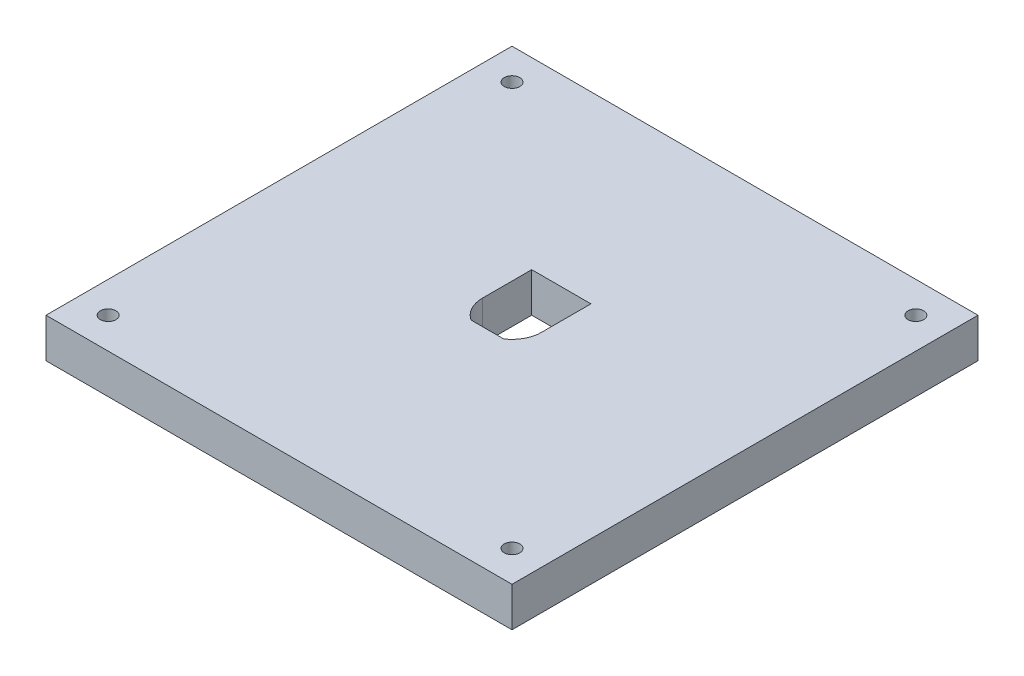
SolidWorks part; units mm, degrees
ref_plane "Front Plane" through (0, 0, 0) normal (0, 0, 1) x (1, 0, 0)
ref_plane "Top Plane" through (0, 0, 0) normal (0, 1, 0) x (1, 0, 0)
ref_plane "Right Plane" through (0, 0, 0) normal (1, 0, 0) x (0, 0, -1)
sketch "Sketch1" plane through (0, 0, 0) normal (0, 1, 0) x (1, 0, 0)
  line L1 (0, 0) -> (150, 0)
  line L2 (0, 0) -> (0, 150)
  line L3 (0, 150) -> (150, 150)
  line L4 (150, 0) -> (150, 150)
  dimension "D1" = 150
  dimension "D2" = 150
extrude "Boss-Extrude1" add sketch "Sketch1" along normal blind 12.7
sketch "Sketch2" plane through (0, 12.7, 0) normal (0, 1, 0) x (1, 0, 0)
  line L0 (75, 150) -> (75, 0) construction
  line L1 (150, 150) -> (0, 150) construction
  line L2 (0, 0) -> (150, 0) construction
  line L3 (0, 75) -> (150, 75) construction
  line L4 (0, 150) -> (0, 0) construction
  line L5 (150, 0) -> (150, 150) construction
  line L7 (84.525, 75) -> (65.475, 75)
  line L8 (84.525, 75) -> (84.525, 90.875)
  line L9 (84.525, 90.875) -> (65.475, 90.875)
  line L10 (65.475, 75) -> (65.475, 90.875)
  line L11 (69.7349, 82.9375) -> (80.2651, 82.9375)
  line L12 (69.7349, 82.9375) -> (69.7349, 67.0625)
  line L13 (69.7349, 67.0625) -> (80.2651, 67.0625)
  line L14 (80.2651, 82.9375) -> (80.2651, 67.0625)
  line L15 (69.7349, 82.9375) -> (80.2651, 67.0625) construction
  line L16 (69.7349, 67.0625) -> (80.2651, 82.9375) construction
  circle A0 centre (75, 75) radius 9.525
  circle A1 centre (10, 140) radius 2.5
  circle A2 centre (140, 140) radius 2.5
  circle A3 centre (140, 10) radius 2.5
  circle A4 centre (10, 10) radius 2.5
  point P22 (75, 67.0625)
  dimension "D1" = 19.05
  dimension "D5" = 5
  dimension "D2" = 19.05
  dimension "D3" = 7.9375
  dimension "D4" = 23.8125
  dimension "D6" = 10
  dimension "D7" = 10
extrude "Cut-Extrude1" cut sketch "Sketch2" against normal blind 12.7 contours A0 L8 L9 L10 | L7 A0 L14 | L12 A0 L7 | L14 L11 L12 L7 | L11 A0 | L14 A0 L7 | L7 A0 L12 | L14 L7 L12 L13 | A1 | A2 | A3 | A4
